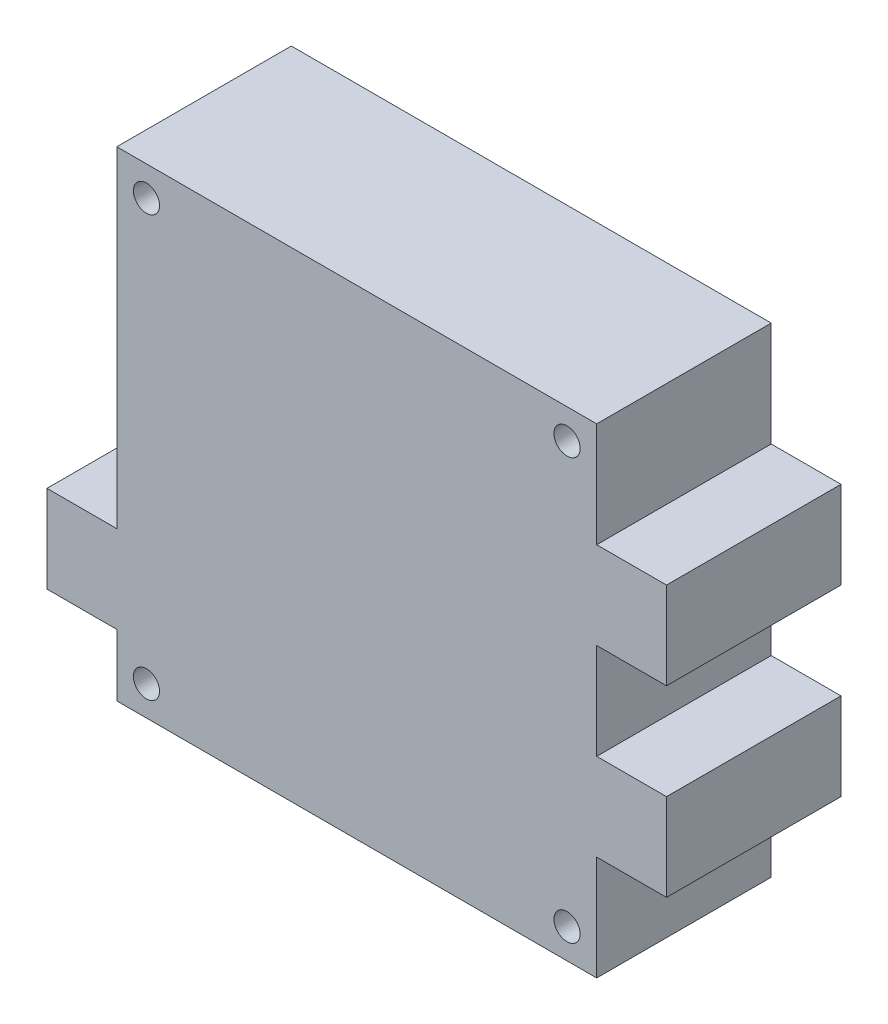
SolidWorks part; units mm, degrees
ref_plane "前视基准面" through (0, 0, 0) normal (0, 0, 1) x (1, 0, 0)
ref_plane "上视基准面" through (0, 0, 0) normal (0, 1, 0) x (1, 0, 0)
ref_plane "右视基准面" through (0, 0, 0) normal (1, 0, 0) x (0, 0, -1)
sketch "草图1" plane through (0, 0, 0) normal (0, 0, 1) x (1, 0, 0)
  line L0 (-27.5, -20.4024) -> (-35.5, -20.4024)
  line L1 (-27.5, 27.5) -> (27.5, 27.5)
  line L3 (-27.5, -27.5) -> (27.5, -27.5)
  line L5 (-27.5, 27.5) -> (27.5, -27.5) construction
  line L6 (-27.5, -27.5) -> (27.5, 27.5) construction
  line L7 (-35.5, -20.4024) -> (-35.5, -10.4024)
  line L8 (-35.5, -10.4024) -> (-27.5, -10.4024)
  line L9 (-27.5, 27.5) -> (-27.5, -10.4024)
  line L10 (-27.5, -20.4024) -> (-27.5, -27.5)
  line L11 (27.5, 27.5) -> (27.5, 15.5)
  line L12 (27.5, -15.5) -> (35.5, -15.5)
  line L13 (35.5, -15.5) -> (35.5, -5.5)
  line L14 (35.5, -5.5) -> (27.5, -5.5)
  line L15 (27.5, 5.5) -> (27.5, -5.5)
  line L16 (27.5, 15.5) -> (35.5, 15.5)
  line L17 (35.5, 15.5) -> (35.5, 5.5)
  line L18 (35.5, 5.5) -> (27.5, 5.5)
  line L19 (27.5, -15.5) -> (27.5, -27.5)
  circle A0 centre (-24.1, 24.1) radius 1.5
  circle A1 centre (24.1, 24.1) radius 1.5
  circle A2 centre (-24.1, -24.1) radius 1.5
  circle A3 centre (24.1, -24.1) radius 1.5
  point P0 (0, 0)
  dimension "D3" = 3
  dimension "D1" = 55
  dimension "D2" = 55
  dimension "D4" = 3.4
  dimension "D5" = 3.4
extrude "凸台-拉伸1" add sketch "草图1" along normal blind 20
